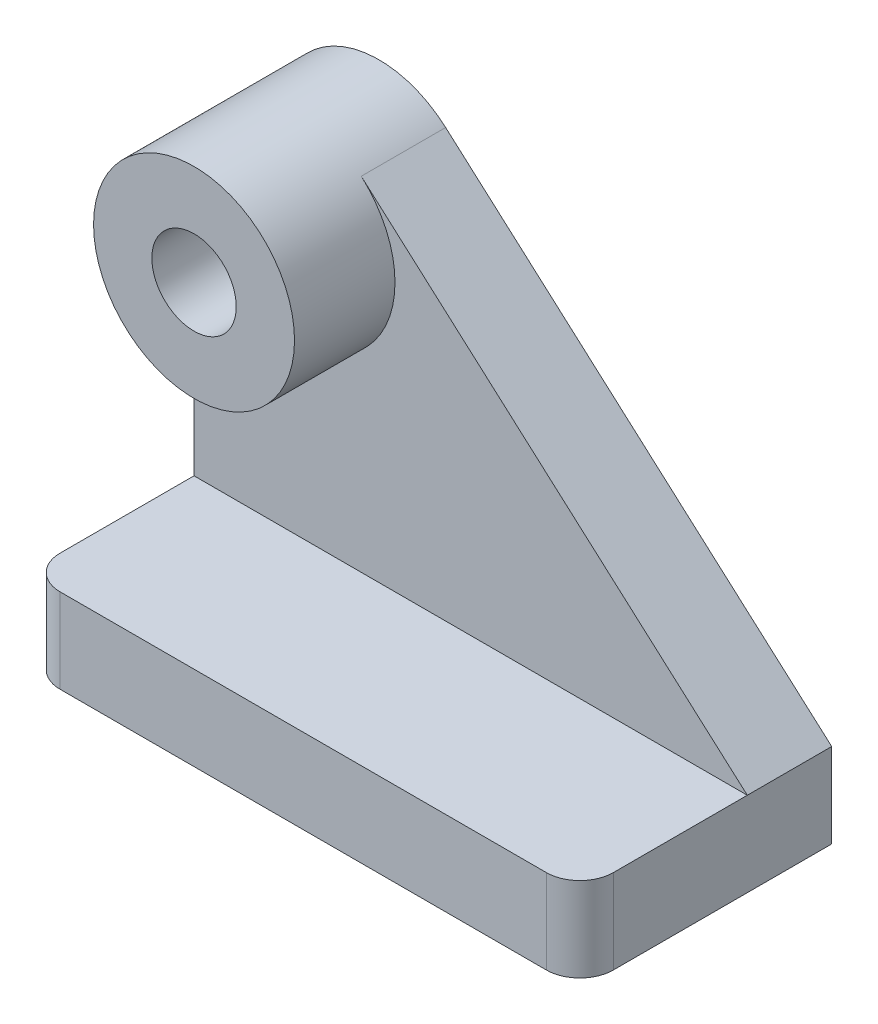
SolidWorks part; units mm, degrees
other "DetailItem1"
material "Zoltek Panex 33"
ref_plane "Frontal" through (0, 0, 0) normal (0, 0, 1) x (1, 0, 0)
ref_plane "Horizontal" through (0, 0, 0) normal (0, 1, 0) x (1, 0, 0)
ref_plane "Profile" through (0, 0, 0) normal (1, 0, 0) x (0, 0, -1)
sketch "Sketch1" plane through (0, 0, 0) normal (0, 1, 0) x (1, 0, 0)
  line L1 (-79.0348, 4.3792) -> (25.8672, 4.3792)
  line L2 (-79.0348, 4.3792) -> (-79.0348, -43.3728)
  line L3 (-79.0348, -43.3728) -> (25.8672, -43.3728)
  line L4 (25.8672, 4.3792) -> (25.8672, -43.3728)
  dimension "D1" = 104.902
  dimension "D2" = 47.752
extrude "Extrude1" add sketch "Sketch1" along normal blind 16.002
fillet "Fillet1" radius 6.35 2 edges at (25.8672, 8.001, 43.3728) (-79.0348, 8.001, 43.3728)
sketch "Sketch2" plane through (0, 16.002, 0) normal (0, 1, 0) x (-1, 0, 0)
  line L0 (-25.8672, 11.6228) -> (79.0348, 11.6228)
  line L1 (-25.8672, 37.0228) -> (-25.8672, -4.3792) construction
  line L2 (79.0348, -4.3792) -> (79.0348, 37.0228) construction
  line L3 (-25.8672, -4.3792) -> (79.0348, -4.3792) construction
  line L8 (79.0348, -4.3792) -> (79.0348, 37.0228)
  line L9 (72.6848, 43.3728) -> (-19.5172, 43.3728)
  line L10 (-25.8672, 37.0228) -> (-25.8672, -4.3792)
  line L11 (-25.8672, -4.3792) -> (79.0348, -4.3792)
  line L12 (79.0348, -4.3792) -> (79.0348, 11.6228)
  line L14 (-25.8672, 11.6228) -> (-25.8672, -4.3792)
  line L15 (-25.8672, -4.3792) -> (79.0348, -4.3792)
  arc A2 (79.0348, 37.0228) -> (72.6848, 43.3728) centre (72.6848, 37.0228) ccw
  arc A3 (-19.5172, 43.3728) -> (-25.8672, 37.0228) centre (-19.5172, 37.0228) ccw
  dimension "D1" = 16.002
  dimension "D2" = 0
extrude "Extrude2" add sketch "Sketch2" along normal blind 69.85
sketch "Sketch3" plane through (0, 0, 11.6228) normal (0, 0, 1) x (1, 0, 0)
  line L0 (25.8672, 85.852) -> (25.8672, 16.002) construction
  line L1 (-72.6848, 16.002) -> (19.5172, 16.002) construction
  line L2 (-47.3314, 81.0425) -> (25.8672, 16.002)
  circle A0 centre (-59.9848, 66.802) radius 19.05
  line M2 (25.8672, 16.002) -> (25.8672, 85.852)
  line M3 (25.8672, 85.852) -> (-79.0348, 85.852)
  dimension "D2" = 38.1
  dimension "D1" = 85.852
  dimension "D3" = 50.8
extrude "Cut-Extrude1" cut sketch "Sketch3" against normal blind 69.85 contours A0 L2 M2 M3
sketch "Sketch4" plane through (0, 0, 11.6228) normal (0, 0, 1) x (1, 0, 0)
  line L4 (-79.0348, 85.852) -> (-79.0348, 16.002) construction
  arc A0 (-59.9848, 85.852) -> (-79.0348, 66.802) centre (-59.9848, 66.802) ccw
extrude "Cut-Extrude3" cut sketch "Sketch4" along normal through all and the other way through all flip side to cut
sketch "Sketch5" plane through (0, 0, 11.6228) normal (0, 0, 1) x (1, 0, 0)
  circle A0 centre (-59.9848, 66.802) radius 19.05
extrude "Extrude3" add sketch "Sketch5" along normal blind 19.05
sketch "Sketch6" plane through (0, 0, 30.6728) normal (0, 0, 1) x (1, 0, 0)
  circle A0 centre (-59.9848, 66.802) radius 8.001
extrude "Cut-Extrude4" cut sketch "Sketch6" against normal through all
